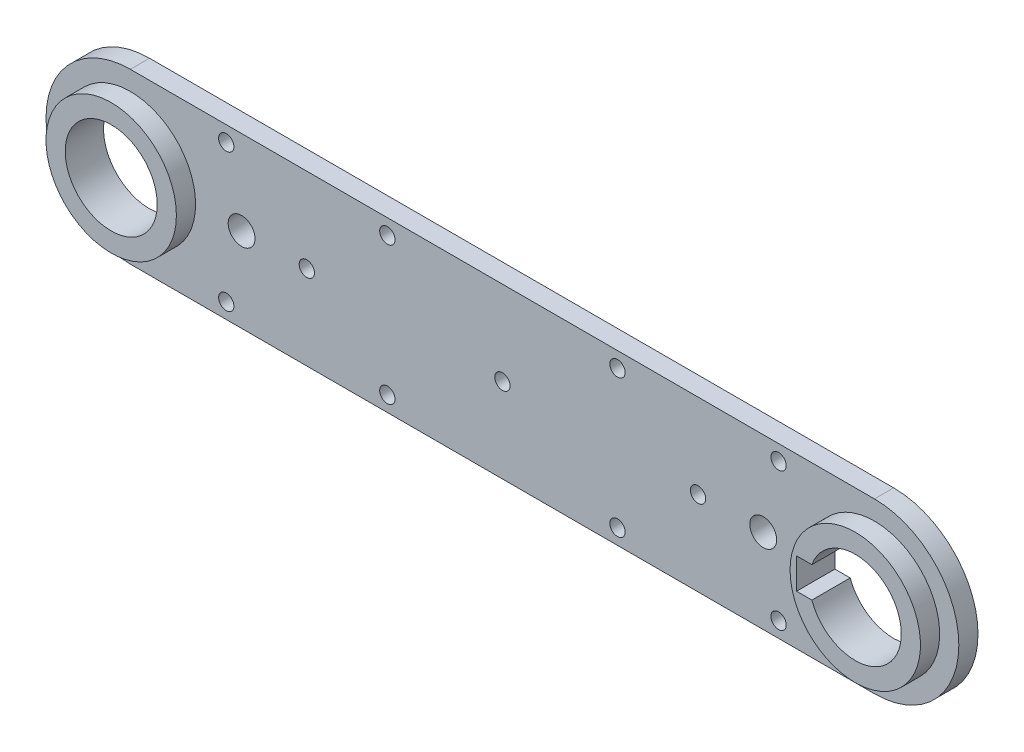
SolidWorks part; units mm, degrees
material "Alloy Steel (SS)"
ref_plane "Front Plane" through (0, 0, 0) normal (0, 0, 1) x (1, 0, 0)
ref_plane "Top Plane" through (0, 0, 0) normal (0, 1, 0) x (1, 0, 0)
ref_plane "Right Plane" through (0, 0, 0) normal (1, 0, 0) x (0, 0, -1)
sketch "Sketch1" plane through (0, 0, 0) normal (0, 0, 1) x (1, 0, 0)
  line L0 (0, 0) -> (194, 0) construction
  line L1 (0, 22) -> (194, 22)
  line L2 (0, -22) -> (194, -22)
  circle A0 centre (0, 0) radius 15
  circle A1 centre (194, 0) radius 15
  circle A2 centre (0, 0) radius 22
  circle A3 centre (194, 0) radius 22
  dimension "D1" = 30
  dimension "D3" = 30
  dimension "D2" = 194
  dimension "D6" = 194
  dimension "D7" = 194
  dimension "D4" = 7
  dimension "D5" = 7
extrude "Boss-Extrude1" add sketch "Sketch1" along normal blind 5 contours L0 A2 L2 A3 | A2 L0 A3 L1
sketch "Sketch2" plane through (0, 0, 5) normal (0, 0, 1) x (1, 0, 0)
  line L0 (97, 22) -> (97, -22) construction
  line L1 (0, 22) -> (194, 22) construction
  line L2 (0, -22) -> (194, -22) construction
  circle A0 centre (0, 0) radius 12
  circle A1 centre (0, 0) radius 17
  circle A2 centre (194, 0) radius 17
  circle A3 centre (194, 0) radius 12
  dimension "D1" = 24
  dimension "D2" = 5
extrude "Boss-Extrude2" add sketch "Sketch2" along normal blind 5
sketch "Sketch3" plane through (0, 0, 5) normal (0, 0, 1) x (1, 0, 0)
  circle A1 centre (194, 0) radius 12
  circle A2 centre (194, 0) radius 12
  circle A3 centre (194, 0) radius 17
  circle A4 centre (194, 0) radius 17
  circle A5 centre (0, 0) radius 17
  circle A6 centre (0, 0) radius 17
  circle A7 centre (0, 0) radius 12
  circle A8 centre (0, 0) radius 12
  dimension "D1" = 0
  dimension "D2" = 0
  dimension "D3" = 0
  dimension "D4" = 0
extrude "Cut-Extrude1" cut sketch "Sketch3" against normal blind 6 contours A8 | A2
sketch "Sketch5" plane through (0, 0, 0) normal (0, 0, -1) x (-1, 0, 0)
  line L0 (0, 0) -> (-194, 0) construction
  line L1 (0, -18) -> (-194, -18) construction
  line L2 (0, 18) -> (-194, 18) construction
  line L3 (0, 22) -> (-194, 22) construction
  line L4 (-97, 22) -> (-97, -22) construction
  line L5 (0, -22) -> (-194, -22) construction
  line L6 (-194, 0) -> (0, 0) construction
  line L7 (-194, 0) -> (-204.2749, 0) construction
  arc A0 (0, -18) -> (0, 18) centre (0, 0) ccw construction
  arc A1 (-194, 18) -> (-194, -18) centre (-194, 0) ccw construction
  circle A2 centre (-169, 18) radius 2
  circle A3 centre (-67, 18) radius 2
  circle A6 centre (-67, -18) radius 2
  circle A7 centre (-169, -18) radius 2
  circle A8 centre (-127, 18) radius 2
  circle A9 centre (-127, -18) radius 2
  circle A10 centre (-25, 18) radius 2
  circle A11 centre (-25, -18) radius 2
  circle A12 centre (-148, 0) radius 2
  circle A13 centre (-97, 0) radius 2
  circle A14 centre (-46, 0) radius 2
  circle A15 centre (-165, 0) radius 3.5
  circle A16 centre (-29, 0) radius 3.5
  point P4 (-97, 0)
  dimension "D2" = 4
  dimension "D5" = 4
  dimension "D6" = 30
  dimension "D7" = 30
  dimension "D9" = 21
  dimension "D11" = 7
  dimension "D12" = 17
  dimension "D1" = 4
  dimension "D3" = 25
  dimension "D4" = 30
  dimension "D8" = 25
  dimension "D10" = 21
sketch "Sketch7" plane through (0, 0, 0) normal (0, 0, -1) x (-1, 0, 0)
  circle A1 centre (-194, -16) radius 1.25
  circle A2 centre (-210, 0) radius 1.25
  circle A3 centre (-194, 16) radius 1.25
  circle A4 centre (-178, 0) radius 1.25
  dimension "D2" = 2.5
  dimension "D3" = 4
extrude "Cut-Extrude2" cut sketch "Sketch5" against normal blind 10
sketch "Sketch8" plane through (0, 0, 0) normal (0, 0, -1) x (-1, 0, 0)
  line L1 (-10.8, -4) -> (-14.8, -4)
  line L2 (-10.8, -4) -> (-10.8, 4)
  line L3 (-10.8, 4) -> (-14.8, 4)
  line L4 (-14.8, -4) -> (-14.8, 4)
  line L5 (-10.8, -4) -> (-14.8, 4) construction
  line L6 (-10.8, 4) -> (-14.8, -4) construction
  point P0 (-12.8, 0)
  dimension "D1" = 14.8
  dimension "D2" = 4
  dimension "D3" = 8
extrude "Cut-Extrude3" [suppressed] cut sketch "Sketch8" against normal up to next
sketch "Sketch9" plane through (0, 0, 0) normal (0, 0, -1) x (-1, 0, 0)
  line L0 (-194, 0) -> (-166.7541, 0) construction
  line L1 (-182.7, -4) -> (-178.7, -4)
  line L2 (-182.7, -4) -> (-182.7, 4)
  line L3 (-182.7, 4) -> (-178.7, 4)
  line L4 (-178.7, -4) -> (-178.7, 4)
  line L5 (-182.7, -4) -> (-178.7, 4) construction
  line L6 (-182.7, 4) -> (-178.7, -4) construction
  circle A0 centre (-194, 0) radius 12 construction
  point P0 (-180.7, 0)
  dimension "D1" = 8
  dimension "4" = 4
  dimension "D3" = 15.3
extrude "Cut-Extrude4" cut sketch "Sketch9" against normal blind 10
sketch "Sketch10" plane through (0, 0, 0) normal (0, 0, -1) x (-1, 0, 0)
  circle A0 centre (0, 0) radius 14 construction
  circle A1 centre (0, 14) radius 1.25
  circle A2 centre (14, 0) radius 1.25
  circle A3 centre (0, -14) radius 1.25
  circle A4 centre (-14, 0) radius 1.25
  dimension "D1" = 28
  dimension "D2" = 2.5
sketch "Sketch11" plane through (0, 0, 0) normal (0, 0, -1) x (-1, 0, 0)
  point P0 (-194, 0)
hole_wizard "M2.5 Tapped Hole1" positions "Sketch12" profile "Sketch13" tap size "M2.5" standard "ISO"
sketch "Sketch12" plane through (0, 0, 0) normal (0, 0, -1) x (-1, 0, 0)
  point P0 (0, 14)
  point P3 (14, 0)
  point P6 (0, -14)
  point P9 (-14, 0)
sketch "Sketch13" plane through (0, 14, 0) normal (1, 0, 0) x (0, 1, 0)
  line L0 (0, 0) -> (0, 6.35)
  line L1 (0, 6.35) -> (1.025, 5.7341)
  line L2 (1.025, 5.7341) -> (1.025, 0)
  line L5 (1.025, 0) -> (0, 0)
  line L10 (0, 6.35) -> (-1.025, 5.7341) construction
  line L11 (0, -6.35) -> (0, 107.95) construction
  dimension "Tap Drill Dia." = 2.05
  dimension "Tap Drill Depth" = 6.35
  dimension "Drill Angle" = 118
